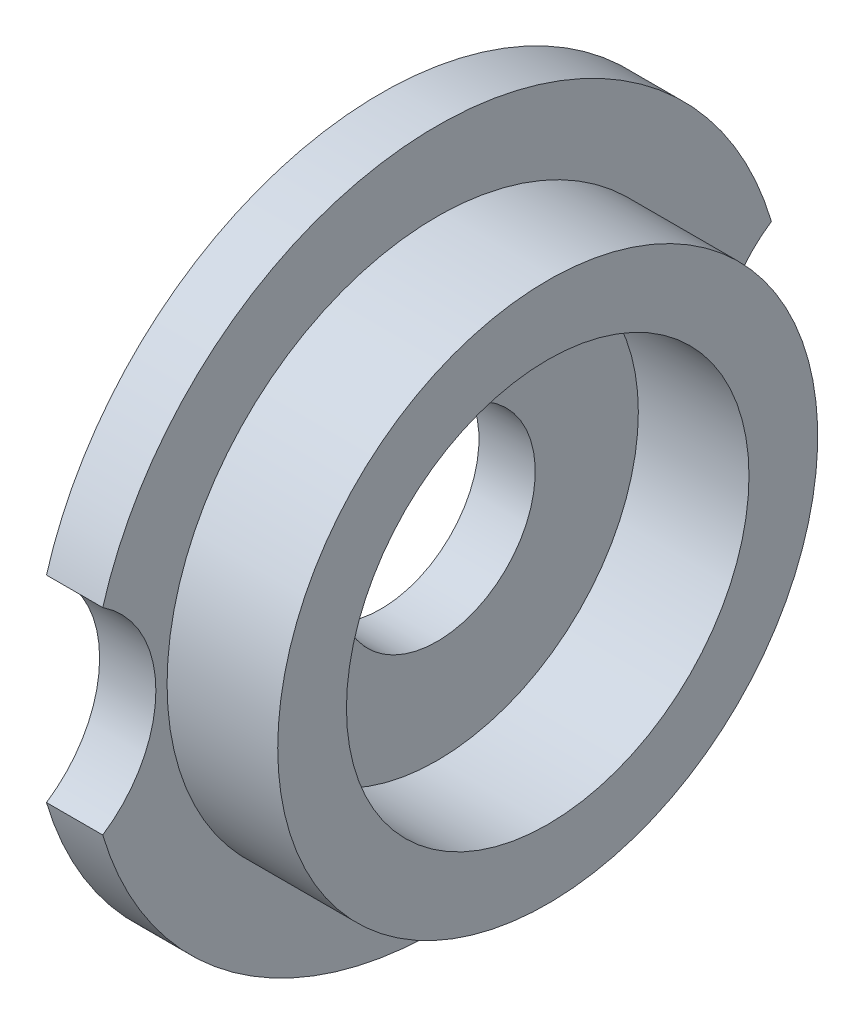
SolidWorks part; units mm, degrees
material "PLA"
ref_plane "Front Plane" through (0, 0, 0) normal (0, 0, 1) x (1, 0, 0)
ref_plane "Top Plane" through (0, 0, 0) normal (0, 1, 0) x (1, 0, 0)
ref_plane "Right Plane" through (0, 0, 0) normal (1, 0, 0) x (0, 0, -1)
sketch "Sketch1" plane through (0, 0, 0) normal (0, 0, 1) x (1, 0, 0)
  line L0 (-2.865, 4.25) -> (-2.865, 17.75)
  line L1 (-2.865, 17.75) -> (0, 17.75)
  line L2 (0, 17.75) -> (0, 13.75)
  line L3 (0, 13.75) -> (5.635, 13.75)
  line L4 (-2.865, 4.25) -> (0, 4.25)
  line L5 (0, 4.25) -> (0, 10.25)
  line L6 (0, 10.25) -> (5.635, 10.25)
  line L7 (5.635, 10.25) -> (5.635, 13.75)
  line L8 (-29.388, 0) -> (46.7239, 0) construction
  dimension "D1" = 4.25
  dimension "D2" = 20.5
  dimension "D3" = 27.5
  dimension "D4" = 35.5
  dimension "D5" = 2.865
  dimension "D6" = 8.5
revolve "Revolve1" add sketch "Sketch1" angle 360 about L8
hole_wizard "M8 Clearance Hole1" positions "Sketch2" profile "Sketch3" hole size "M8" standard "ANSI Metric" end condition up to next
sketch "Sketch2" plane through (-2.865, 0, 0) normal (-1, 0, 0) x (0, 0, 1)
  point P0 (0, 0)
sketch "Sketch3" plane through (-2.865, 0, 0) normal (0, 1, 0) x (0, 0, 1)
  line L0 (0, 0) -> (0, 8.5)
  line L1 (0, 8.5) -> (5, 8.5)
  line L2 (5, 8.5) -> (5, 0)
  line L5 (5, 0) -> (0, 0)
  line L11 (0, -6.35) -> (0, 107.95) construction
  dimension "Thru Hole Dia." = 10
  dimension "Thru Hole Depth" = 8.5
sketch "Sketch4" plane through (-2.865, 0, 0) normal (-1, 0, 0) x (0, 0, 1)
  line L0 (-20.32, 0) -> (20.32, 0) construction
  circle A0 centre (0, 0) radius 20.32 construction
  circle A1 centre (-20.32, 0) radius 6
  circle A2 centre (20.32, 0) radius 6
  dimension "D1" = 40.64
  dimension "D2" = 12
extrude "Cut-Extrude1" cut sketch "Sketch4" against normal blind 10
